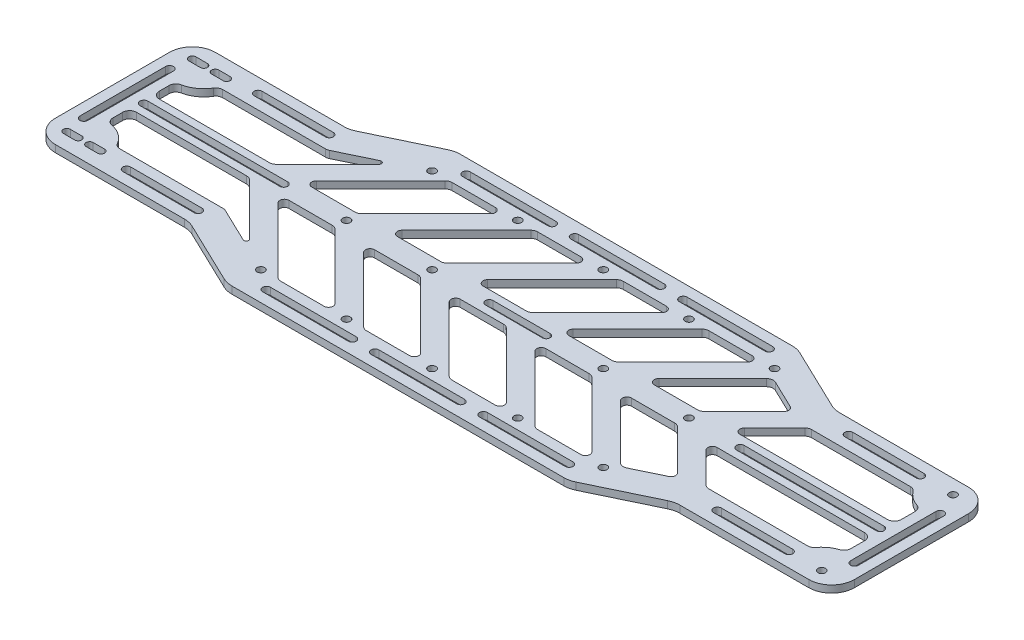
SolidWorks part; units mm, degrees
material "6061-T6 (SS)"
ref_plane "Front Plane" through (0, 0, 0) normal (0, 0, 1) x (1, 0, 0)
ref_plane "Top Plane" through (0, 0, 0) normal (0, 1, 0) x (1, 0, 0)
ref_plane "Right Plane" through (0, 0, 0) normal (1, 0, 0) x (0, 0, -1)
sketch "Sketch1" plane through (0, 0, 0) normal (0, 1, 0) x (1, 0, 0)
  line L1 (0, 0) -> (355.6, 0)
  line L2 (0, 0) -> (0, 101.6)
  line L3 (0, 101.6) -> (355.6, 101.6)
  line L4 (355.6, 0) -> (355.6, 101.6)
  dimension "D1" = 355.6
  dimension "D2" = 101.6
extrude "Boss-Extrude1" add sketch "Sketch1" along normal blind 3.175
sketch "Sketch2" plane through (0, 0, 0) normal (0, -1, 0) x (1, 0, 0)
  line L0 (0, -50.8) -> (355.6, -50.8) construction
  line L1 (0, -101.6) -> (0, 0) construction
  line L2 (355.6, 0) -> (355.6, -101.6) construction
  point P6 (10.16, -22.86)
  point P7 (344.8634, -21.59)
  point P8 (344.8634, -80.01)
  point P9 (10.16, -78.74)
  dimension "D1" = 55.88
  dimension "D2" = 58.42
  dimension "D3" = 334.7034
  dimension "D4" = 10.16
hole_wizard "M3 Clearance Hole2" positions "Sketch6" profile "Sketch5" hole size "M3" standard "ANSI Metric" end condition through all
sketch "Sketch6" plane through (0, 0, 0) normal (0, -1, 0) x (-1, 0, 0)
  point P0 (-344.8634, 21.59)
  point P3 (-344.8634, 80.01)
sketch "Sketch5" plane through (344.8634, 0, -21.59) normal (1, 0, 0) x (0, 0, -1)
  line L0 (0, 0) -> (0, 3.175)
  line L1 (0, 3.175) -> (1.7, 3.175)
  line L2 (1.7, 3.175) -> (1.7, 0)
  line L5 (1.7, 0) -> (0, 0)
  line L11 (0, -6.35) -> (0, 107.95) construction
  dimension "Thru Hole Dia." = 3.4
  dimension "Thru Hole Depth" = 3.175
sketch "Sketch7" plane through (0, 0, 0) normal (0, -1, 0) x (1, 0, 0)
  line L0 (7.62, -22.86) -> (12.7, -22.86) construction
  line L1 (7.62, -21.2838) -> (12.7, -21.2838)
  line L2 (7.62, -24.4362) -> (12.7, -24.4362)
  line L3 (0, -50.8) -> (34.1188, -50.8) construction
  line L4 (0, -50.8) -> (355.6, -50.8) construction
  line L5 (7.62, -78.74) -> (12.7, -78.74) construction
  line L6 (7.62, -80.3162) -> (12.7, -80.3162)
  line L7 (7.62, -77.1638) -> (12.7, -77.1638)
  arc A0 (7.62, -21.2838) -> (7.62, -24.4362) centre (7.62, -22.86) ccw
  arc A1 (12.7, -24.4362) -> (12.7, -21.2838) centre (12.7, -22.86) ccw
  arc A2 (7.62, -80.3162) -> (7.62, -77.1638) centre (7.62, -78.74) cw
  arc A3 (12.7, -77.1638) -> (12.7, -80.3162) centre (12.7, -78.74) cw
  point P2 (10.16, -22.86)
  point P15 (10.16, -78.74)
  dimension "D1" = 1.5762
  dimension "D2" = 5.08
extrude "Cut-Extrude1" cut sketch "Sketch7" against normal through all
sketch "Sketch16" plane through (0, 3.175, 0) normal (0, 1, 0) x (1, 0, 0)
  line L0 (355.6, 15.24) -> (285.75, 15.24)
  line L1 (355.6, 0) -> (355.6, 101.6) construction
  line L2 (0, 0) -> (355.6, 0) construction
  line L3 (355.6, 15.24) -> (355.6, 0)
  line L4 (355.6, 0) -> (254, 0)
  line L5 (285.75, 15.24) -> (254, 0)
  line L6 (355.6, 50.8) -> (0, 50.8) construction
  line L7 (0, 101.6) -> (0, 0) construction
  line L8 (177.8, 0) -> (177.8, 101.6) construction
  line L9 (355.6, 101.6) -> (0, 101.6) construction
  line L10 (69.85, 15.24) -> (101.6, 0)
  line L11 (0, 0) -> (101.6, 0)
  line L12 (0, 15.24) -> (0, 0)
  line L13 (0, 15.24) -> (69.85, 15.24)
  line L14 (0, 86.36) -> (69.85, 86.36)
  line L15 (0, 86.36) -> (0, 101.6)
  line L16 (0, 101.6) -> (101.6, 101.6)
  line L17 (69.85, 86.36) -> (101.6, 101.6)
  line L18 (285.75, 86.36) -> (254, 101.6)
  line L19 (355.6, 101.6) -> (254, 101.6)
  line L20 (355.6, 86.36) -> (355.6, 101.6)
  line L21 (355.6, 86.36) -> (285.75, 86.36)
  dimension "D1" = 15.24
  dimension "D2" = 101.6
  dimension "D3" = 69.85
extrude "Cut-Extrude3" cut sketch "Sketch16" against normal through all
fillet "Fillet1" radius 10.16 12 edges at (0, 1.5875, -86.36) (69.85, 1.5875, -86.36) (101.6, 1.5875, -101.6) (254, 1.5875, -101.6) (285.75, 1.5875, -86.36) (355.6, 1.5875, -86.36) (0, 1.5875, -15.24) (69.85, 1.5875, -15.24) (101.6, 1.5875, 0) (254, 1.5875, 0) (285.75, 1.5875, -15.24) (355.6, 1.5875, -15.24)
sketch "Sketch17" plane through (0, 3.175, 0) normal (0, 1, 0) x (1, 0, 0)
  line L0 (0, 50.8) -> (355.6, 50.8) construction
  line L1 (142.24, 88.9) -> (104.14, 50.8) construction
  line L2 (0, 50.8) -> (355.6, 50.8) construction
  line L3 (0, 76.2) -> (0, 25.4) construction
  line L4 (111.76, 88.9) -> (78.74, 55.88)
  line L5 (78.74, 55.88) -> (104.14, 55.88)
  line L6 (104.14, 55.88) -> (137.16, 88.9)
  line L7 (137.16, 88.9) -> (111.76, 88.9)
  line L8 (104.14, 88.9) -> (142.24, 88.9) construction
  line L9 (78.74, 45.72) -> (104.14, 45.72)
  line L10 (104.14, 45.72) -> (137.16, 12.7)
  line L11 (137.16, 12.7) -> (111.76, 12.7)
  line L12 (111.76, 12.7) -> (78.74, 45.72)
  line L13 (175.26, 88.9) -> (149.86, 88.9)
  line L14 (149.86, 88.9) -> (116.84, 55.88)
  line L15 (142.24, 55.88) -> (175.26, 88.9)
  line L16 (116.84, 55.88) -> (142.24, 55.88)
  line L17 (116.84, 45.72) -> (142.24, 45.72)
  line L18 (142.24, 45.72) -> (175.26, 12.7)
  line L19 (149.86, 12.7) -> (116.84, 45.72)
  line L20 (175.26, 12.7) -> (149.86, 12.7)
  line L21 (213.36, 88.9) -> (187.96, 88.9)
  line L22 (187.96, 88.9) -> (154.94, 55.88)
  line L23 (180.34, 55.88) -> (213.36, 88.9)
  line L24 (154.94, 55.88) -> (180.34, 55.88)
  line L25 (154.94, 45.72) -> (180.34, 45.72)
  line L26 (180.34, 45.72) -> (213.36, 12.7)
  line L27 (187.96, 12.7) -> (154.94, 45.72)
  line L28 (213.36, 12.7) -> (187.96, 12.7)
  line L29 (251.46, 88.9) -> (226.06, 88.9)
  line L30 (226.06, 88.9) -> (193.04, 55.88)
  line L31 (218.44, 55.88) -> (251.46, 88.9)
  line L32 (193.04, 55.88) -> (218.44, 55.88)
  line L33 (193.04, 45.72) -> (218.44, 45.72)
  line L34 (218.44, 45.72) -> (251.46, 12.7)
  line L35 (226.06, 12.7) -> (193.04, 45.72)
  line L36 (251.46, 12.7) -> (226.06, 12.7)
  line L37 (260.0411, 84.7811) -> (231.14, 55.88)
  line L38 (231.14, 55.88) -> (256.54, 55.88)
  line L39 (256.54, 55.88) -> (277.2032, 76.5432)
  line L40 (277.2032, 76.5432) -> (260.0411, 84.7811)
  line L41 (256.0844, 100.5995) -> (283.6656, 87.3605) construction
  line L42 (231.14, 45.72) -> (256.54, 45.72)
  line L43 (260.0411, 16.8189) -> (231.14, 45.72)
  line L44 (256.54, 45.72) -> (277.2032, 25.0568)
  line L45 (277.2032, 25.0568) -> (260.0411, 16.8189)
  line L46 (287.02, 73.66) -> (269.24, 55.88)
  line L47 (269.24, 55.88) -> (342.9, 55.88)
  line L48 (342.9, 55.88) -> (342.9, 67.4627)
  line L49 (287.02, 73.66) -> (333.8649, 73.66)
  line L51 (288.0621, 86.36) -> (345.44, 86.36) construction
  line L52 (355.6, 25.4) -> (355.6, 76.2) construction
  line L53 (269.24, 45.72) -> (342.9, 45.72)
  line L54 (342.9, 45.72) -> (342.9, 34.1373)
  line L55 (287.02, 27.94) -> (333.8649, 27.94)
  line L56 (287.02, 27.94) -> (269.24, 45.72)
  line L57 (12.7, 55.88) -> (66.04, 55.88)
  line L58 (66.04, 55.88) -> (86.36, 76.2)
  line L59 (72.7401, 73.66) -> (24.3397, 73.66)
  line L60 (12.7, 66.04) -> (12.7, 55.88)
  line L61 (10.16, 86.36) -> (67.5379, 86.36) construction
  line L62 (86.36, 76.2) -> (94.0476, 83.8876)
  line L63 (94.0476, 83.8876) -> (72.7401, 73.66)
  line L64 (71.9344, 87.3605) -> (99.5156, 100.5995) construction
  line L65 (12.7, 45.72) -> (66.04, 45.72)
  line L66 (86.36, 25.4) -> (94.0476, 17.7124)
  line L67 (66.04, 45.72) -> (86.36, 25.4)
  line L68 (94.0476, 17.7124) -> (72.7401, 27.94)
  line L69 (72.7401, 27.94) -> (24.3397, 27.94)
  line L70 (12.7, 35.56) -> (12.7, 45.72)
  arc A0 (342.9, 67.4627) -> (333.8649, 73.66) centre (344.8634, 80.01) cw
  circle A1 centre (344.8634, 80.01) radius 1.7 construction
  arc A2 (342.9, 34.1373) -> (333.8649, 27.94) centre (344.8634, 21.59) ccw
  arc A3 (24.3397, 73.66) -> (12.7, 66.04) centre (12.7, 78.74) cw
  arc A4 (12.7, 77.1638) -> (12.7, 80.3162) centre (12.7, 78.74) ccw construction
  arc A5 (24.3397, 27.94) -> (12.7, 35.56) centre (12.7, 22.86) ccw
  point P4 (104.14, 88.9)
  point P8 (104.14, 50.8)
  point P9 (104.14, 12.7)
  point P12 (142.24, 88.9)
  point P13 (142.24, 50.8)
  point P14 (142.24, 12.7)
  point P15 (180.34, 88.9)
  point P16 (180.34, 50.8)
  point P17 (180.34, 12.7)
  point P18 (218.44, 88.9)
  point P19 (218.44, 50.8)
  point P20 (218.44, 12.7)
  point P21 (256.54, 88.9)
  point P22 (256.54, 50.8)
  point P23 (256.54, 12.7)
  dimension "D13" = 12.7
  dimension "D17" = 12.7
  dimension "D1" = 38.1
  dimension "D2" = 104.14
  dimension "D4" = 45
  dimension "D5" = 5.08
  dimension "D6" = 25.4
  dimension "D7" = 7.62
  dimension "D9" = 38.1
  dimension "D10" = 38.1
  dimension "D11" = 12.7
  dimension "D12" = 12.7
  dimension "D14" = 12.7
  dimension "D15" = 12.7
  dimension "D16" = 38.1
  dimension "D18" = 12.7
  dimension "D19" = 38.1
  dimension "D3" = 5
  dimension "D8" = 4
hole_wizard "M3 Clearance Hole5" positions "Sketch19" profile "Sketch18" hole size "M3" standard "ANSI Metric" end condition through all
sketch "Sketch19" plane through (0, 3.175, 0) normal (0, 1, 0) x (1, 0, 0)
  point P0 (104.14, 88.9)
  point P3 (142.24, 88.9)
  point P6 (180.34, 88.9)
  point P9 (218.44, 88.9)
  point P12 (256.54, 88.9)
  point P15 (256.54, 12.7)
  point P18 (218.44, 12.7)
  point P21 (180.34, 12.7)
  point P24 (142.24, 12.7)
  point P27 (104.14, 12.7)
  point P30 (104.14, 50.8)
  point P33 (256.54, 50.8)
  point P36 (142.24, 50.8)
  point P39 (180.34, 50.8)
  point P42 (218.44, 50.8)
sketch "Sketch18" plane through (104.14, 3.175, -88.9) normal (1, 0, 0) x (0, 0, 1)
  line L0 (0, 0) -> (0, 3.175)
  line L1 (0, 3.175) -> (1.7, 3.175)
  line L2 (1.7, 3.175) -> (1.7, 0)
  line L5 (1.7, 0) -> (0, 0)
  line L11 (0, -6.35) -> (0, 107.95) construction
  dimension "Thru Hole Dia." = 3.4
  dimension "Thru Hole Depth" = 3.175
extrude "Cut-Extrude4" cut sketch "Sketch17" against normal through all
fillet "Fillet2" radius 2.032 16 edges at (137.16, 1.5875, -12.7) (175.26, 1.5875, -12.7) (213.36, 1.5875, -12.7) (251.46, 1.5875, -12.7) (251.46, 1.5875, -88.9) (213.36, 1.5875, -88.9) (175.26, 1.5875, -88.9) (137.16, 1.5875, -88.9) (193.04, 1.5875, -45.72) (154.94, 1.5875, -45.72) (116.84, 1.5875, -45.72) (78.74, 1.5875, -45.72) (193.04, 1.5875, -55.88) (154.94, 1.5875, -55.88) (116.84, 1.5875, -55.88) (78.74, 1.5875, -55.88)
fillet "Fillet3" radius 3.048 16 edges at (226.06, 1.5875, -12.7) (218.44, 1.5875, -45.72) (180.34, 1.5875, -45.72) (187.96, 1.5875, -12.7) (149.86, 1.5875, -12.7) (111.76, 1.5875, -12.7) (142.24, 1.5875, -45.72) (104.14, 1.5875, -45.72) (218.44, 1.5875, -55.88) (180.34, 1.5875, -55.88) (142.24, 1.5875, -55.88) (104.14, 1.5875, -55.88) (226.06, 1.5875, -88.9) (187.96, 1.5875, -88.9) (149.86, 1.5875, -88.9) (111.76, 1.5875, -88.9)
fillet "Fillet4" radius 3.048 5 edges at (72.7401, 1.5875, -73.66) (66.04, 1.5875, -55.88) (12.7, 1.5875, -55.88) (12.7, 1.5875, -66.04) (24.3397, 1.5875, -73.66)
fillet "Fillet5" radius 3.048 5 edges at (12.7, 1.5875, -35.56) (24.3397, 1.5875, -27.94) (72.7401, 1.5875, -27.94) (66.04, 1.5875, -45.72) (12.7, 1.5875, -45.72)
fillet "Fillet6" radius 3.048 12 edges at (342.9, 1.5875, -45.72) (342.9, 1.5875, -55.88) (342.9, 1.5875, -34.1373) (333.8649, 1.5875, -27.94) (342.9, 1.5875, -67.4627) (333.8649, 1.5875, -73.66) (287.02, 1.5875, -27.94) (287.02, 1.5875, -73.66) (260.0411, 1.5875, -84.7811) (256.54, 1.5875, -55.88) (256.54, 1.5875, -45.72) (260.0411, 1.5875, -16.8189)
fillet "Fillet7" radius 2.032 6 edges at (277.2032, 1.5875, -76.5432) (277.2032, 1.5875, -25.0568) (231.14, 1.5875, -55.88) (231.14, 1.5875, -45.72) (269.24, 1.5875, -55.88) (269.24, 1.5875, -45.72)
fillet "Fillet8" radius 1.016 2 edges at (94.0476, 1.5875, -83.8876) (94.0476, 1.5875, -17.7124)
sketch "Sketch20" plane through (0, 3.175, 0) normal (0, 1, 0) x (1, 0, 0)
  line L0 (167.64, 50.8) -> (193.04, 50.8) construction
  line L1 (0, 50.8) -> (355.6, 50.8) construction
  line L2 (167.64, 52.5) -> (193.04, 52.5)
  line L3 (167.64, 49.1) -> (193.04, 49.1)
  arc A0 (167.64, 52.5) -> (167.64, 49.1) centre (167.64, 50.8) ccw
  arc A1 (193.04, 49.1) -> (193.04, 52.5) centre (193.04, 50.8) ccw
  circle A2 centre (180.34, 50.8) radius 1.7 construction
  point P5 (180.34, 50.8)
  dimension "D1" = 25.4
extrude "Cut-Extrude5" cut sketch "Sketch20" against normal through all
pattern_linear "LPattern1" count 2 spacing 10.16 along (1, 0, 0) of "Cut-Extrude1"
sketch "Sketch22" plane through (0, 3.175, 0) normal (0, 1, 0) x (1, 0, 0)
  line L0 (13.97, 50.8) -> (76.2, 50.8) construction
  line L1 (0, 50.8) -> (355.6, 50.8) construction
  line L2 (13.97, 52.55) -> (76.2, 52.55)
  line L3 (13.97, 49.05) -> (76.2, 49.05)
  line L4 (0, 76.2) -> (0, 25.4) construction
  arc A0 (13.97, 52.55) -> (13.97, 49.05) centre (13.97, 50.8) ccw
  arc A1 (76.2, 49.05) -> (76.2, 52.55) centre (76.2, 50.8) ccw
  point P4 (45.085, 50.8)
  dimension "D3" = 76.2
  dimension "D1" = 3.5
  dimension "D2" = 13.97
extrude "Cut-Extrude6" cut sketch "Sketch22" against normal through all
sketch "Sketch23" plane through (0, 3.175, 0) normal (0, 1, 0) x (1, 0, 0)
  line L0 (279.4, 50.8) -> (341.63, 50.8) construction
  line L1 (0, 50.8) -> (355.6, 50.8) construction
  line L2 (279.4, 52.55) -> (341.63, 52.55)
  line L3 (279.4, 49.05) -> (341.63, 49.05)
  line L4 (355.6, 25.4) -> (355.6, 76.2) construction
  arc A0 (279.4, 52.55) -> (279.4, 49.05) centre (279.4, 50.8) ccw
  arc A1 (341.63, 49.05) -> (341.63, 52.55) centre (341.63, 50.8) ccw
  point P4 (310.515, 50.8)
  dimension "D2" = 13.97
  dimension "D3" = 76.2
  dimension "D1" = 3.5
extrude "Cut-Extrude7" cut sketch "Sketch23" against normal through all
sketch "Sketch24" plane through (0, 3.175, 0) normal (0, 1, 0) x (1, 0, 0)
  line L0 (6.35, 69.85) -> (6.35, 31.75) construction
  line L1 (0, 50.8) -> (355.6, 50.8) construction
  line L2 (8.1, 69.85) -> (8.1, 31.75)
  line L3 (4.6, 69.85) -> (4.6, 31.75)
  line L4 (349.25, 69.85) -> (349.25, 31.75) construction
  line L5 (351, 69.85) -> (351, 31.75)
  line L6 (347.5, 69.85) -> (347.5, 31.75)
  line L7 (0, 76.2) -> (0, 25.4) construction
  line L8 (355.6, 25.4) -> (355.6, 76.2) construction
  arc A0 (8.1, 69.85) -> (4.6, 69.85) centre (6.35, 69.85) ccw
  arc A1 (4.6, 31.75) -> (8.1, 31.75) centre (6.35, 31.75) ccw
  arc A2 (351, 69.85) -> (347.5, 69.85) centre (349.25, 69.85) ccw
  arc A3 (347.5, 31.75) -> (351, 31.75) centre (349.25, 31.75) ccw
  point P4 (6.35, 50.8)
  point P10 (349.25, 50.8)
  dimension "D1" = 3.5
  dimension "D2" = 38.1
  dimension "D3" = 6.35
  dimension "D4" = 6.35
extrude "Cut-Extrude8" cut sketch "Sketch24" against normal through all
sketch "Sketch25" plane through (0, 3.175, 0) normal (0, 1, 0) x (1, 0, 0)
  line L0 (101.3472, 95.25) -> (256.2857, 95.25) construction
  line L1 (251.6879, 101.6) -> (103.9121, 101.6) construction
  line L2 (113.03, 95.25) -> (151.13, 95.25) construction
  line L3 (113.03, 97) -> (151.13, 97)
  line L4 (113.03, 93.5) -> (151.13, 93.5)
  line L5 (161.29, 95.25) -> (199.39, 95.25) construction
  line L6 (161.29, 97) -> (199.39, 97)
  line L7 (161.29, 93.5) -> (199.39, 93.5)
  line L8 (209.55, 95.25) -> (247.65, 95.25) construction
  line L9 (209.55, 97) -> (247.65, 97)
  line L10 (209.55, 93.5) -> (247.65, 93.5)
  line L11 (0, 76.2) -> (0, 25.4) construction
  arc A0 (113.03, 97) -> (113.03, 93.5) centre (113.03, 95.25) ccw
  arc A1 (151.13, 93.5) -> (151.13, 97) centre (151.13, 95.25) ccw
  arc A2 (161.29, 97) -> (161.29, 93.5) centre (161.29, 95.25) ccw
  arc A3 (199.39, 93.5) -> (199.39, 97) centre (199.39, 95.25) ccw
  arc A4 (209.55, 97) -> (209.55, 93.5) centre (209.55, 95.25) ccw
  arc A5 (247.65, 93.5) -> (247.65, 97) centre (247.65, 95.25) ccw
  point P6 (132.08, 95.25)
  point P11 (180.34, 95.25)
  point P18 (228.6, 95.25)
  dimension "D3" = 10.16
  dimension "D4" = 10.16
  dimension "D5" = 113.03
  dimension "D1" = 6.35
  dimension "D2" = 38.1
  dimension "D6" = 3.5
extrude "Cut-Extrude9" cut sketch "Sketch25" against normal through all
ref_plane "Plane1" through (0, 0, -50.8) normal (0, 0, -1) x (-1, 0, 0)
mirror "Mirror1" about plane through (0, 0, -50.8) normal (0, 0, -1) of "Cut-Extrude9"
sketch "Sketch26" plane through (0, 3.175, 0) normal (0, 1, 0) x (1, 0, 0)
  line L0 (26.8574, 80.01) -> (337.2378, 80.01) construction
  line L1 (35.56, 80.01) -> (67.31, 80.01) construction
  line L2 (35.56, 81.76) -> (67.31, 81.76)
  line L3 (35.56, 78.26) -> (67.31, 78.26)
  line L4 (298.45, 80.01) -> (330.2, 80.01) construction
  line L5 (298.45, 81.76) -> (330.2, 81.76)
  line L6 (298.45, 78.26) -> (330.2, 78.26)
  line L7 (10.16, 86.36) -> (67.5379, 86.36) construction
  line L8 (0, 76.2) -> (0, 25.4) construction
  line L9 (355.6, 25.4) -> (355.6, 76.2) construction
  arc A0 (35.56, 81.76) -> (35.56, 78.26) centre (35.56, 80.01) ccw
  arc A1 (67.31, 78.26) -> (67.31, 81.76) centre (67.31, 80.01) ccw
  arc A2 (298.45, 81.76) -> (298.45, 78.26) centre (298.45, 80.01) ccw
  arc A3 (330.2, 78.26) -> (330.2, 81.76) centre (330.2, 80.01) ccw
  point P4 (51.435, 80.01)
  point P9 (314.325, 80.01)
  dimension "D4" = 35.56
  dimension "D5" = 25.4
  dimension "D1" = 31.75
  dimension "D2" = 3.5
  dimension "D3" = 6.35
extrude "Cut-Extrude10" cut sketch "Sketch26" against normal through all
mirror "Mirror2" about plane through (0, 0, -50.8) normal (0, 0, -1) of "Cut-Extrude10"
